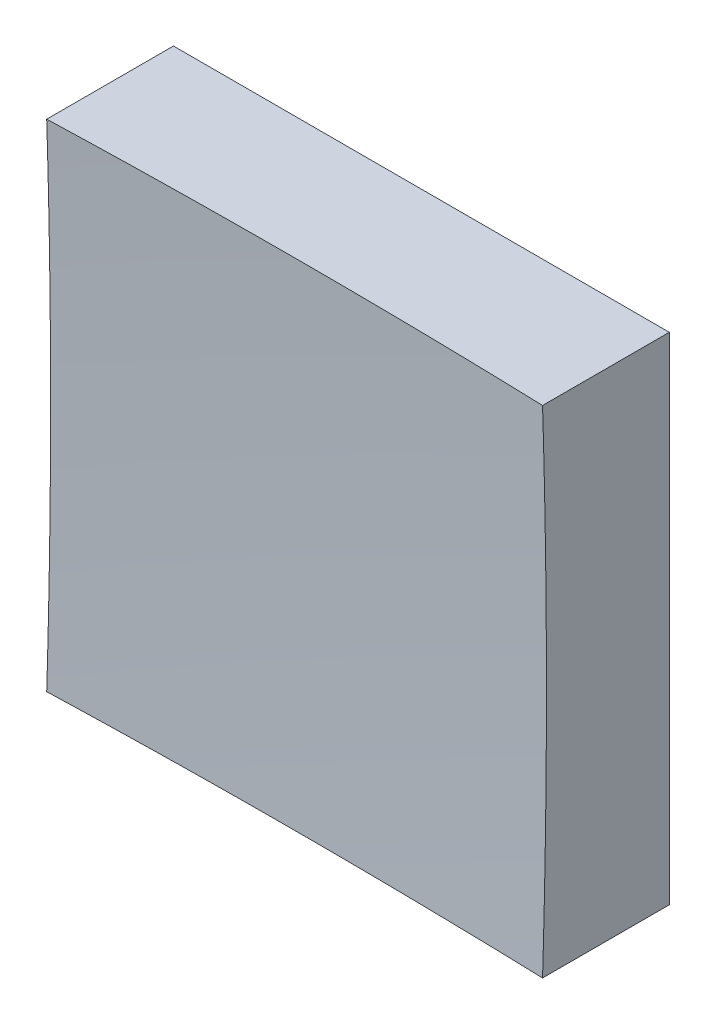
SolidWorks part; units mm, degrees
ref_plane "前视基准面" through (0, 0, 0) normal (0, 0, 1) x (1, 0, 0)
ref_plane "上视基准面" through (0, 0, 0) normal (0, 1, 0) x (1, 0, 0)
ref_plane "右视基准面" through (0, 0, 0) normal (1, 0, 0) x (0, 0, -1)
sketch "草图1" plane through (0, 0, 0) normal (0, 0, 1) x (1, 0, 0)
  line L1 (-12.5, 12.5) -> (12.5, 12.5)
  line L2 (-12.5, 12.5) -> (-12.5, -12.5)
  line L3 (-12.5, -12.5) -> (12.5, -12.5)
  line L4 (12.5, 12.5) -> (12.5, -12.5)
  line L5 (-12.5, 12.5) -> (12.5, -12.5) construction
  line L6 (-12.5, -12.5) -> (12.5, 12.5) construction
  point P0 (0, 0)
  dimension "D1" = 25
  dimension "D2" = 25
extrude "凸台-拉伸1" add sketch "草图1" along normal blind 20 contours L2 L3 L4 L1
sketch "草图2" plane through (0, 0, 0) normal (0, 1, 0) x (1, 0, 0)
  line L0 (-7.4603, -6) -> (7.3192, -6) construction
  line L1 (0, 0) -> (0, -12.1749) construction
  line L2 (389.9382, -316.8473) -> (0, -316.8473)
  line L3 (0, -316.8473) -> (0, -6)
  arc A1 (389.9382, -316.8473) -> (0, -6) centre (0, -406) ccw
  dimension "D2" = 800
  dimension "D1" = 6
revolve "切除-旋转2" cut sketch "草图2" angle 360 about L3
